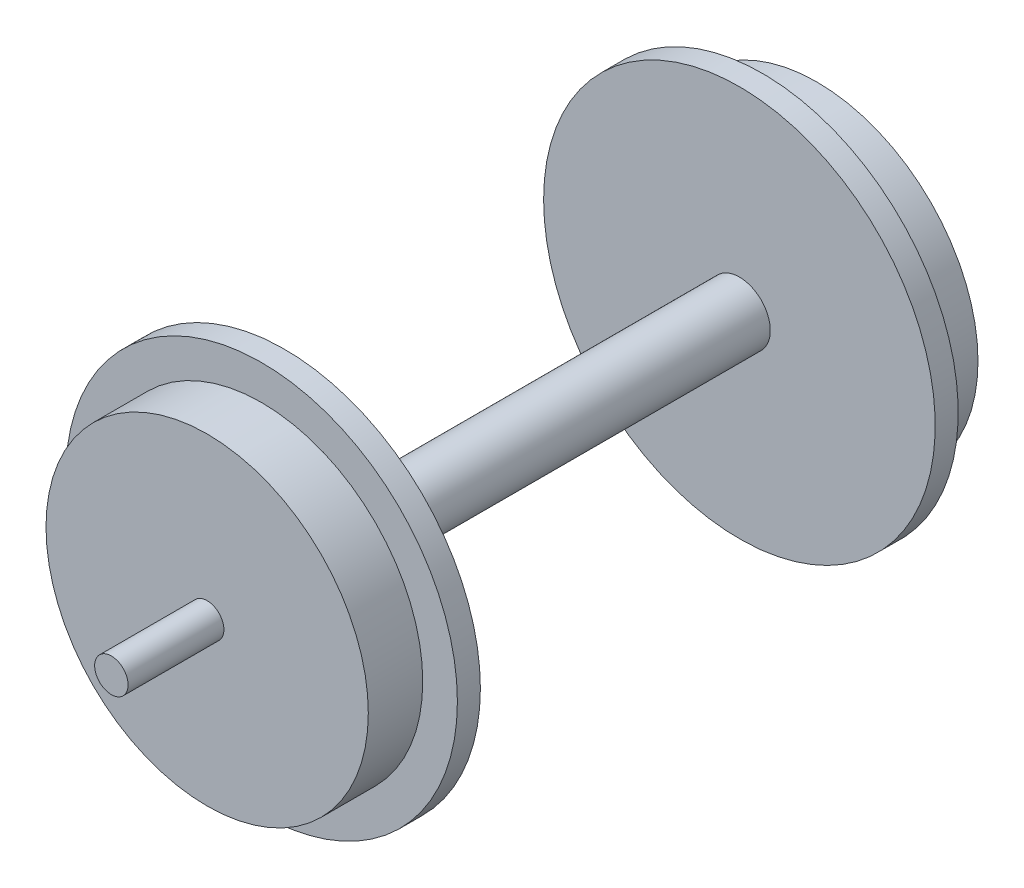
SolidWorks part; units mm, degrees
ref_plane "Front" through (0, 0, 0) normal (0, 0, 1) x (1, 0, 0)
ref_plane "Top" through (0, 0, 0) normal (0, 1, 0) x (1, 0, 0)
ref_plane "Right" through (0, 0, 0) normal (1, 0, 0) x (0, 0, -1)
sketch "Sketch1" plane through (0, 0, 0) normal (0, 0, 1) x (1, 0, 0)
  circle A0 centre (0, 0) radius 17.375
  dimension "D1" = 34.75
extrude "Boss-Extrude1" add sketch "Sketch1" along normal blind 2.04
sketch "Sketch2" plane through (0, 0, 2.04) normal (0, 0, 1) x (1, 0, 0)
  circle A0 centre (0, 0) radius 14.3
  dimension "D1" = 28.6
extrude "Boss-Extrude2" add sketch "Sketch2" along normal blind 4.83
sketch "Sketch3" plane through (0, 0, 0) normal (0, 0, -1) x (-1, 0, 0)
  circle A0 centre (0, 0) radius 2.74
  dimension "D1" = 5.48
extrude "Boss-Extrude3" add sketch "Sketch3" along normal blind 40.36
sketch "Sketch4" plane through (0, 0, -40.36) normal (0, 0, -1) x (-1, 0, 0)
  circle A0 centre (0, 0) radius 17.375
  dimension "D1" = 34.75
extrude "Boss-Extrude4" add sketch "Sketch4" along normal blind 2.04
sketch "Sketch5" plane through (0, 0, -42.4) normal (0, 0, -1) x (-1, 0, 0)
  circle A0 centre (0, 0) radius 14.3
  dimension "D1" = 28.6
extrude "Boss-Extrude5" add sketch "Sketch5" along normal blind 4.83
sketch "Sketch6" plane through (0, 0, -47.23) normal (0, 0, -1) x (-1, 0, 0)
  circle A0 centre (0, 0) radius 1.485
  dimension "D1" = 2.97
extrude "Boss-Extrude6" add sketch "Sketch6" along normal blind 8.5
sketch "Sketch7" plane through (0, 0, 6.87) normal (0, 0, 1) x (1, 0, 0)
  circle A0 centre (0, 0) radius 1.485
  dimension "D1" = 2.97
extrude "Boss-Extrude7" add sketch "Sketch7" along normal blind 8.5
sketch "Sketch8" plane through (0, 0, -42.4) normal (0, 0, -1) x (-1, 0, 0)
  line L0 (-17.375, 0) -> (-17.375, -32.5375)
  circle A0 centre (0, 0) radius 17.375 construction
  point P0 (-17.375, 0)
